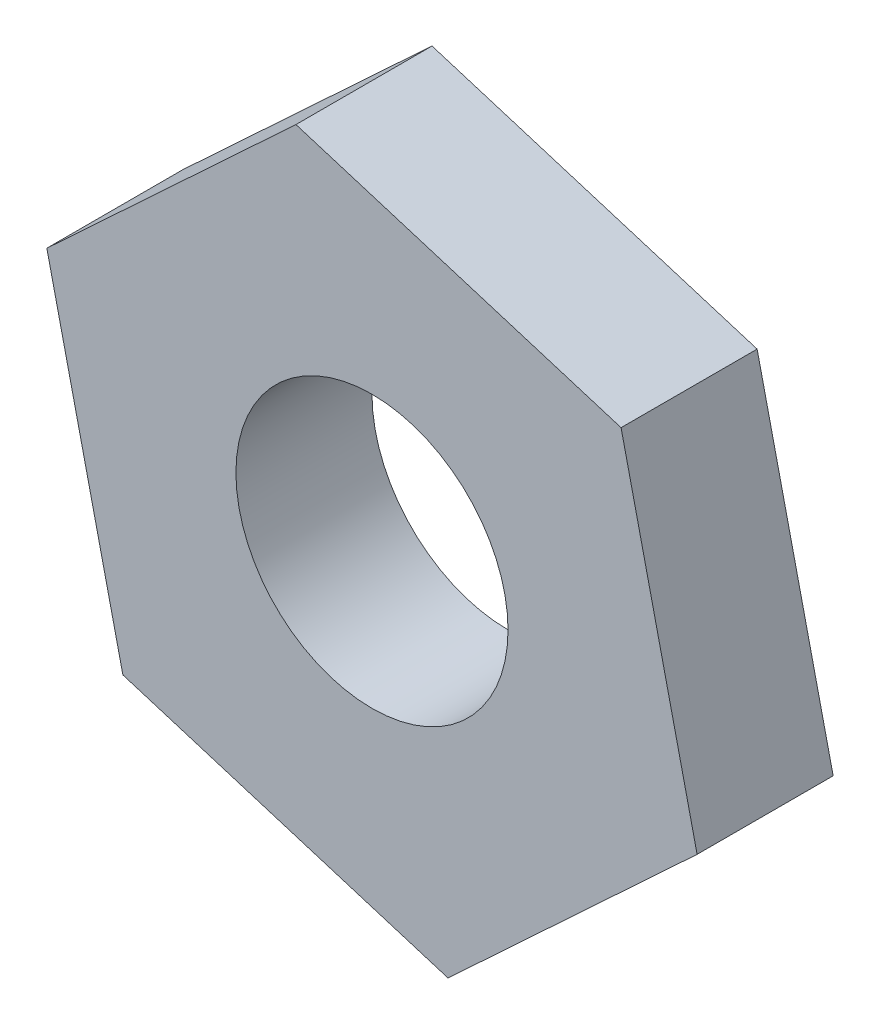
SolidWorks part; units mm, degrees
ref_plane "前视基准面" through (0, 0, 0) normal (0, 0, 1) x (1, 0, 0)
ref_plane "上视基准面" through (0, 0, 0) normal (0, 1, 0) x (1, 0, 0)
ref_plane "右视基准面" through (0, 0, 0) normal (1, 0, 0) x (0, 0, -1)
sketch "草图1" plane through (0, 0, 0) normal (0, 0, 1) x (1, 0, 0)
  line L1 (-9.5588, 2.9376) -> (-7.3235, -6.8093)
  line L2 (-7.3235, -6.8093) -> (2.2353, -9.747)
  line L3 (2.2353, -9.747) -> (9.5588, -2.9376)
  line L4 (9.5588, -2.9376) -> (7.3235, 6.8093)
  line L5 (7.3235, 6.8093) -> (-2.2353, 9.747)
  line L6 (-2.2353, 9.747) -> (-9.5588, 2.9376)
  circle A0 centre (0, 0) radius 8.6603 construction
  dimension "D1" = 10
extrude "凸台-拉伸1" add sketch "草图1" along normal blind 4
sketch "草图2" plane through (0, 0, 4) normal (0, 0, 1) x (1, 0, 0)
  circle A0 centre (0, 0) radius 4
  dimension "D1" = 8
extrude "切除-拉伸1" cut sketch "草图2" against normal through all
